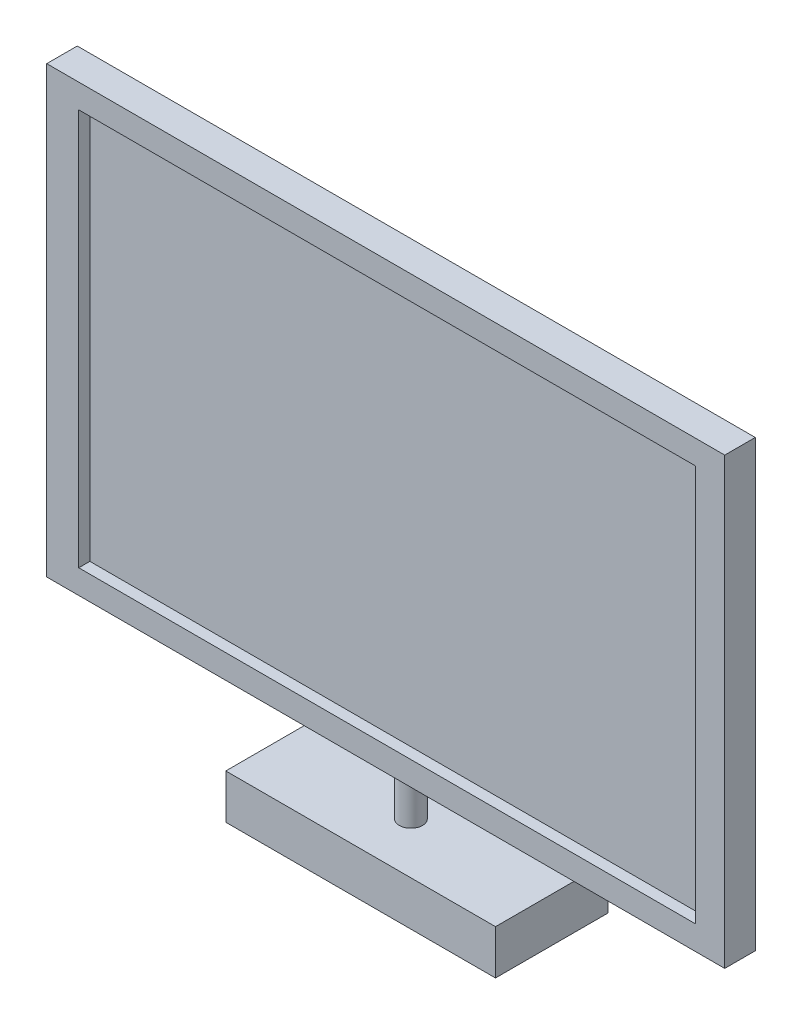
SolidWorks part; units mm, degrees
ref_plane "Alzado" through (0, 0, 0) normal (0, 0, 1) x (1, 0, 0)
ref_plane "Planta" through (0, 0, 0) normal (0, 1, 0) x (1, 0, 0)
ref_plane "Vista lateral" through (0, 0, 0) normal (1, 0, 0) x (0, 0, -1)
sketch "Croquis1" plane through (0, 0, 0) normal (1, 0, 0) x (0, 0, -1)
  line L1 (0, 0) -> (24.7273, 0)
  line L2 (0, 0) -> (0, 360)
  line L3 (0, 360) -> (24.7273, 360)
  line L4 (24.7273, 0) -> (24.7273, 360)
  dimension "D1" = 360
extrude "Saliente-Extruir1" add sketch "Croquis1" along normal blind 549
sketch "Croquis3" plane through (0, 0, 0) normal (0, 0, 1) x (1, 0, 0)
  line L1 (25.9209, 340.5706) -> (525.2344, 340.5706)
  line L2 (25.9209, 340.5706) -> (25.9209, 19.4294)
  line L3 (25.9209, 19.4294) -> (525.2344, 19.4294)
  line L4 (525.2344, 340.5706) -> (525.2344, 19.4294)
extrude "Cortar-Extruir1" cut sketch "Croquis3" against normal blind 9
sketch "Croquis4" plane through (0, 0, 0) normal (0, -1, 0) x (1, 0, 0)
  circle A0 centre (280.9982, -13.9038) radius 9.4037
extrude "Saliente-Extruir2" add sketch "Croquis4" along normal blind 36
sketch "Croquis5" plane through (0, -36, 0) normal (0, -1, 0) x (1, 0, 0)
  line L1 (172.482, 27.5096) -> (390.8867, 27.5096)
  line L2 (172.482, 27.5096) -> (172.482, -63.7319)
  line L3 (172.482, -63.7319) -> (390.8867, -63.7319)
  line L4 (390.8867, 27.5096) -> (390.8867, -63.7319)
extrude "Saliente-Extruir3" add sketch "Croquis5" along normal blind 36
